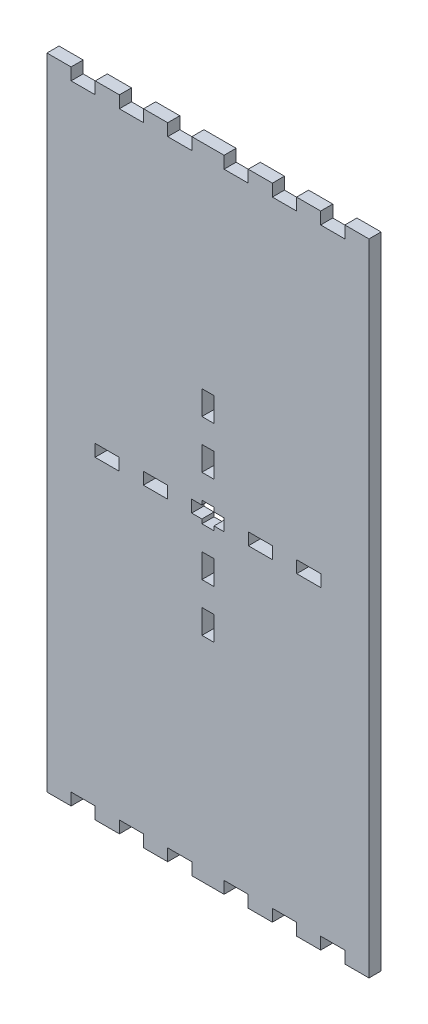
SolidWorks part; units mm, degrees
ref_plane "Front Plane" through (0, 0, 0) normal (0, 0, 1) x (1, 0, 0)
ref_plane "Top Plane" through (0, 0, 0) normal (0, 1, 0) x (1, 0, 0)
ref_plane "Right Plane" through (0, 0, 0) normal (1, 0, 0) x (0, 0, -1)
sketch "Sketch1" plane through (0, 0, 0) normal (0, 0, 1) x (1, 0, 0)
  line L0 (-116.337, 0) -> (135.9707, 0) construction
  line L1 (0, 97.2161) -> (0, -93.9927) construction
  line L2 (-1.5034, 2.54) -> (1.5034, 2.54)
  line L3 (-34, 76.5) -> (-28, 76.5)
  line L4 (-40, 76.5) -> (-40, -76.5)
  line L6 (40, 76.5) -> (40, -76.5)
  line L7 (34, -76.5) -> (28, -76.5)
  line L8 (4, -76.5) -> (4, -79.5)
  line L9 (0, 2.54) -> (0.0026, 2.54)
  line L11 (-4.04, 1.5) -> (-1.5034, 1.5)
  line L12 (-1.5034, 1.5) -> (-1.5034, 2.54)
  line L14 (1.5034, -2.54) -> (-1.5034, -2.54)
  line L15 (-1.5034, -1.5) -> (-1.5034, -2.54)
  line L16 (-4.04, -1.5) -> (-1.5034, -1.5)
  line L17 (4.04, -1.5) -> (1.5034, -1.5)
  line L18 (1.5034, -1.5) -> (1.5034, -2.54)
  line L19 (-4.04, 1.5) -> (-4.04, -1.5)
  line L20 (4.04, 1.5) -> (4.04, -1.5)
  line L21 (1.5034, 1.5) -> (1.5034, 2.54)
  line L22 (4.04, 1.5) -> (1.5034, 1.5)
  line L25 (28.04, 1.5) -> (28.04, -1.5)
  line L26 (-10.04, 1.5) -> (-16.04, 1.5)
  line L27 (-10.04, 1.5) -> (-10.04, -1.5)
  line L28 (-10.04, -1.5) -> (-16.04, -1.5)
  line L29 (-16.04, 1.5) -> (-16.04, -1.5)
  line L30 (-22.04, 1.5) -> (-28.04, 1.5)
  line L31 (-22.04, 1.5) -> (-22.04, -1.5)
  line L32 (-22.04, -1.5) -> (-28.04, -1.5)
  line L33 (-28.04, 1.5) -> (-28.04, -1.5)
  line L34 (22.04, -1.5) -> (28.04, -1.5)
  line L35 (22.04, 1.5) -> (22.04, -1.5)
  line L36 (22.04, 1.5) -> (28.04, 1.5)
  line L37 (16.04, 1.5) -> (16.04, -1.5)
  line L38 (10.04, -1.5) -> (16.04, -1.5)
  line L39 (10.04, 1.5) -> (10.04, -1.5)
  line L40 (10.04, 1.5) -> (16.04, 1.5)
  line L41 (-1.5, -20.54) -> (-1.5, -26.54)
  line L42 (-1.5, 8.54) -> (1.5, 8.54)
  line L43 (-1.5, 8.54) -> (-1.5, 14.54)
  line L44 (-1.5, 14.54) -> (1.5, 14.54)
  line L45 (1.5, 8.54) -> (1.5, 14.54)
  line L46 (1.5, 20.54) -> (-1.5, 20.54)
  line L47 (1.5, 20.54) -> (1.5, 26.54)
  line L48 (1.5, 26.54) -> (-1.5, 26.54)
  line L49 (-1.5, 20.54) -> (-1.5, 26.54)
  line L50 (1.5, -26.54) -> (-1.5, -26.54)
  line L51 (1.5, -20.54) -> (1.5, -26.54)
  line L52 (1.5, -20.54) -> (-1.5, -20.54)
  line L53 (1.5, -8.54) -> (1.5, -14.54)
  line L54 (-1.5, -14.54) -> (1.5, -14.54)
  line L55 (-1.5, -8.54) -> (-1.5, -14.54)
  line L56 (-1.5, -8.54) -> (1.5, -8.54)
  line L57 (-4, 76.5) -> (-4, 79.5)
  line L59 (-40, 76.5) -> (-40, 79.5)
  line L60 (-40, 79.5) -> (-34, 79.5)
  line L61 (-34, 76.5) -> (-34, 79.5)
  line L63 (-28, 76.5) -> (-28, 79.5)
  line L64 (-28, 79.5) -> (-22, 79.5)
  line L65 (-22, 76.5) -> (-22, 79.5)
  line L66 (-4, 79.5) -> (0, 79.5)
  line L67 (-22, 76.5) -> (-16, 76.5)
  line L68 (-16, 76.5) -> (-16, 79.5)
  line L69 (-16, 79.5) -> (-10, 79.5)
  line L70 (-10, 79.5) -> (-10, 76.5)
  line L71 (-10, 76.5) -> (-4, 76.5)
  line L72 (40, 76.5) -> (40, 79.5)
  line L73 (10, 76.5) -> (4, 76.5)
  line L74 (10, 79.5) -> (10, 76.5)
  line L75 (16, 79.5) -> (10, 79.5)
  line L76 (16, 76.5) -> (16, 79.5)
  line L77 (22, 76.5) -> (16, 76.5)
  line L78 (4, 79.5) -> (0, 79.5)
  line L79 (22, 76.5) -> (22, 79.5)
  line L80 (28, 79.5) -> (22, 79.5)
  line L81 (28, 76.5) -> (28, 79.5)
  line L82 (34, 76.5) -> (34, 79.5)
  line L83 (40, 79.5) -> (34, 79.5)
  line L84 (4, 76.5) -> (4, 79.5)
  line L85 (34, 76.5) -> (28, 76.5)
  line L86 (40, -79.5) -> (34, -79.5)
  line L87 (34, -76.5) -> (34, -79.5)
  line L88 (28, -76.5) -> (28, -79.5)
  line L89 (28, -79.5) -> (22, -79.5)
  line L90 (22, -76.5) -> (22, -79.5)
  line L91 (4, -79.5) -> (0, -79.5)
  line L92 (22, -76.5) -> (16, -76.5)
  line L93 (16, -76.5) -> (16, -79.5)
  line L94 (16, -79.5) -> (10, -79.5)
  line L95 (10, -79.5) -> (10, -76.5)
  line L96 (10, -76.5) -> (4, -76.5)
  line L97 (40, -76.5) -> (40, -79.5)
  line L98 (-10, -76.5) -> (-4, -76.5)
  line L99 (-10, -79.5) -> (-10, -76.5)
  line L100 (-16, -79.5) -> (-10, -79.5)
  line L101 (-16, -76.5) -> (-16, -79.5)
  line L102 (-22, -76.5) -> (-16, -76.5)
  line L103 (-4, -79.5) -> (0, -79.5)
  line L104 (-22, -76.5) -> (-22, -79.5)
  line L105 (-28, -79.5) -> (-22, -79.5)
  line L106 (-28, -76.5) -> (-28, -79.5)
  line L107 (-34, -76.5) -> (-34, -79.5)
  line L108 (-40, -79.5) -> (-34, -79.5)
  line L109 (-40, -76.5) -> (-40, -79.5)
  line L110 (-4, -76.5) -> (-4, -79.5)
  line L111 (-34, -76.5) -> (-28, -76.5)
  point P5 (0, 0)
  point P28 (0, 2.54)
  point P71 (-2, 79.5)
  point P72 (-40, 78)
  point P73 (-22, 78)
  point P78 (-16, 78)
  dimension "D1" = 80
  dimension "D3" = 1.5
  dimension "D5" = 1.5034
  dimension "D7" = 6
  dimension "D8" = 6
  dimension "D9" = 2.54
  dimension "D10" = 6
  dimension "D11" = 3
  dimension "D12" = 3
  dimension "D13" = 1.5
  dimension "D14" = 1.5
  dimension "D15" = 3
  dimension "D16" = 1.5
  dimension "D17" = 6
  dimension "D18" = 6
  dimension "D19" = 6
  dimension "D20" = 6
  dimension "D21" = 3
  dimension "D22" = 1.5
  dimension "D23" = 3
  dimension "D24" = 3
  dimension "D25" = 3
  dimension "D27" = 6
  dimension "D28" = 6
  dimension "D29" = 6
  dimension "D30" = 6
  dimension "D31" = 6
  dimension "D32" = 4
  dimension "D33" = 3
  dimension "D34" = 79.5
extrude "Boss-Extrude1" add sketch "Sketch1" along normal blind 3
